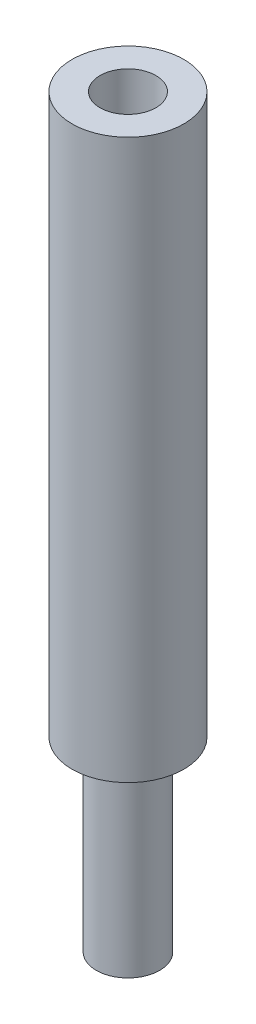
SolidWorks part; units mm, degrees
ref_plane "Front Plane" through (0, 0, 0) normal (0, 0, 1) x (1, 0, 0)
ref_plane "Top Plane" through (0, 0, 0) normal (0, 1, 0) x (1, 0, 0)
ref_plane "Right Plane" through (0, 0, 0) normal (1, 0, 0) x (0, 0, -1)
sketch "Sketch1" plane through (0, 0, 0) normal (0, 1, 0) x (1, 0, 0)
  circle A0 centre (0, 0) radius 1.7
extrude "Boss-Extrude1" add sketch "Sketch1" along normal blind 10
sketch "Sketch2" plane through (0, 10, 0) normal (0, 1, 0) x (1, 0, 0)
  circle A0 centre (0, 0) radius 3
extrude "Boss-Extrude2" add sketch "Sketch2" along normal blind 30
sketch "Sketch3" plane through (0, 40, 0) normal (0, 1, 0) x (1, 0, 0)
  circle A0 centre (0, 0) radius 1.5
extrude "Cut-Extrude1" cut sketch "Sketch3" against normal blind 8
